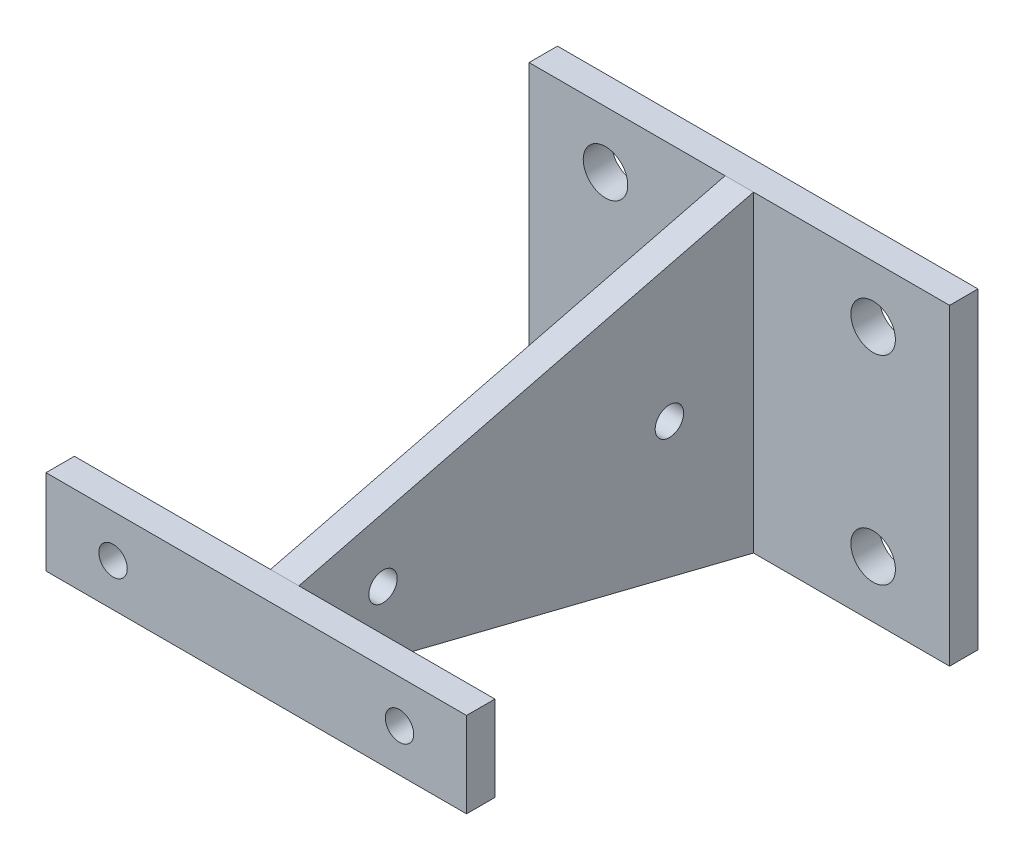
SolidWorks part; units mm, degrees
ref_plane "Front Plane" through (0, 0, 0) normal (0, 0, 1) x (1, 0, 0)
ref_plane "Top Plane" through (0, 0, 0) normal (0, 1, 0) x (1, 0, 0)
ref_plane "Right Plane" through (0, 0, 0) normal (1, 0, 0) x (0, 0, -1)
sketch "Sketch1" plane through (0, 0, 0) normal (0, 0, 1) x (1, 0, 0)
  line L0 (-23.495, 0) -> (-16.002, 0) construction
  line L1 (23.495, 4.7625) -> (-23.495, 4.7625)
  line L2 (23.495, 4.7625) -> (23.495, -4.7625)
  line L3 (23.495, -4.7625) -> (-23.495, -4.7625)
  line L4 (-23.495, 4.7625) -> (-23.495, -4.7625)
  line L5 (23.495, 4.7625) -> (-23.495, -4.7625) construction
  line L6 (23.495, -4.7625) -> (-23.495, 4.7625) construction
  line L7 (-16.002, 0) -> (16.002, 0) construction
  line L8 (16.002, 0) -> (23.495, 0) construction
  circle A0 centre (-16.002, 0) radius 1.5875
  circle A1 centre (16.002, 0) radius 1.5875
  point P0 (0, 0)
  point P5 (0, 0)
  dimension "D2" = 3.175
  dimension "D1" = 32.004
  dimension "D3" = 4.7625
  dimension "D5" = 46.99
extrude "Boss-Extrude1" add sketch "Sketch1" along normal blind 3.175
sketch "Sketch2" plane through (0, 0, 0) normal (1, 0, 0) x (0, 0, -1)
  line L0 (0, 0) -> (9.398, 0) construction
  line L1 (50.8, 17.4625) -> (0, 4.7625)
  line L2 (50.8, 17.4625) -> (50.8, -17.4625)
  line L3 (50.8, -17.4625) -> (0, -4.7625)
  line L4 (0, 4.7625) -> (0, -4.7625)
  line L7 (9.398, 0) -> (41.402, 0) construction
  line L8 (41.402, 0) -> (50.8, 0) construction
  line L10 (0, -4.7625) -> (0, 4.7625) construction
  circle A0 centre (9.398, 0) radius 1.5875
  circle A1 centre (41.402, 0) radius 1.5875
  point P0 (0, -4.7625)
  point P11 (0, 0)
  point P12 (27.0561, 2.443)
  point P15 (50.8, 0)
  dimension "D2" = 3.175
  dimension "D1" = 32.004
  dimension "D4" = 50.8
  dimension "D5" = 34.925
extrude "Boss-Extrude2" add sketch "Sketch2" along normal mid plane 3.175
sketch "Sketch4" plane through (0, 0, -50.8) normal (0, 0, -1) x (-1, 0, 0)
  line L0 (23.495, 4.7625) -> (23.495, -4.7625) construction
  line L1 (-23.495, 17.4625) -> (23.495, 17.4625)
  line L2 (-23.495, 17.4625) -> (-23.495, -17.4625)
  line L3 (-23.495, -17.4625) -> (23.495, -17.4625)
  line L4 (23.495, 17.4625) -> (23.495, -17.4625)
  line L5 (-23.495, 17.4625) -> (23.495, -17.4625) construction
  line L6 (-23.495, -17.4625) -> (23.495, 17.4625) construction
  line L7 (-23.495, 4.7625) -> (-1.5875, 4.7625) construction
  line L9 (14.9514, 11.1125) -> (-14.9514, 11.1125) construction
  line L10 (14.9514, 11.1125) -> (14.9514, -11.1125) construction
  line L11 (14.9514, -11.1125) -> (-14.9514, -11.1125) construction
  line L12 (-14.9514, 11.1125) -> (-14.9514, -11.1125) construction
  line L13 (14.9514, 11.1125) -> (-14.9514, -11.1125) construction
  line L14 (14.9514, -11.1125) -> (-14.9514, 11.1125) construction
  circle A0 centre (-14.9514, 11.1125) radius 2.4892
  circle A1 centre (14.9514, 11.1125) radius 2.4892
  circle A2 centre (14.9514, -11.1125) radius 2.4892
  circle A3 centre (-14.9514, -11.1125) radius 2.4892
  point P0 (0, 0)
  point P10 (0, 0)
  dimension "D2" = 4.9784
  dimension "D1" = 12.7
  dimension "D3" = 6.35
extrude "Boss-Extrude3" add sketch "Sketch4" along normal blind 3.175
